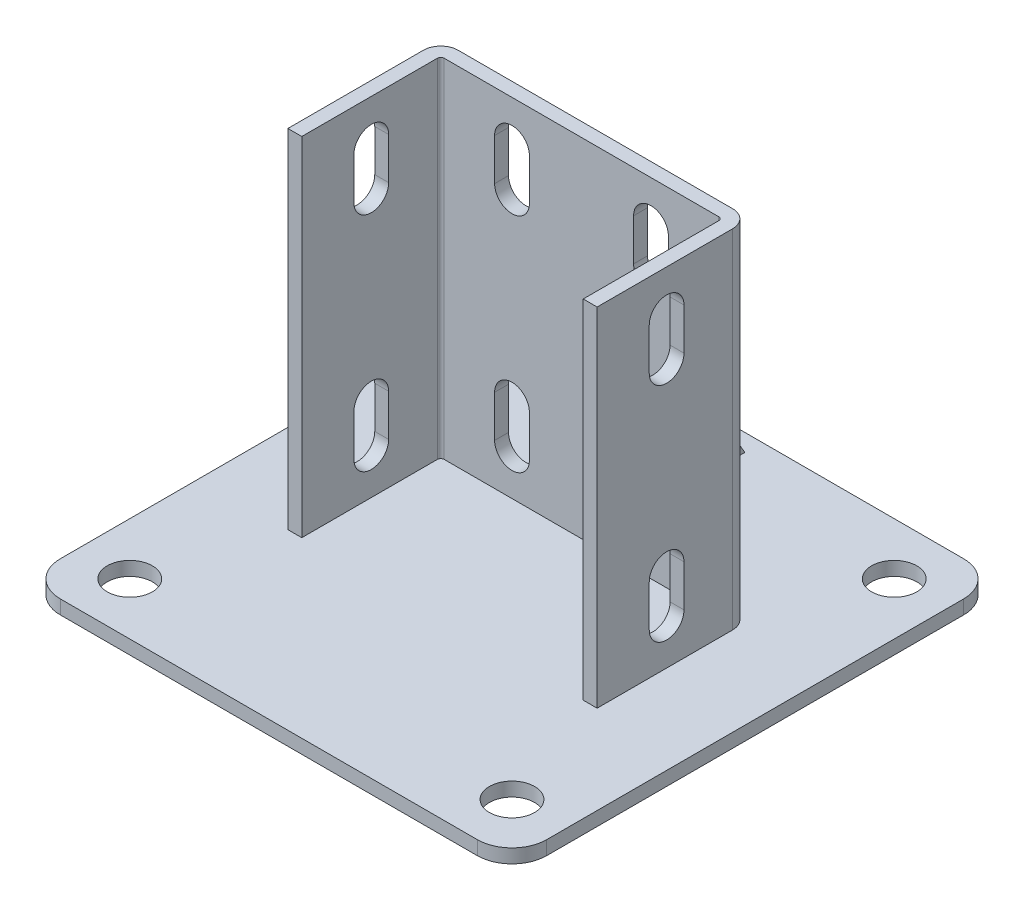
SolidWorks part; units mm, degrees
material "Ст3пс ГОСТ 380-2005"
ref_plane "Спереди" through (0, 0, 0) normal (0, 0, 1) x (1, 0, 0)
ref_plane "Сверху" through (0, 0, 0) normal (0, 1, 0) x (1, 0, 0)
ref_plane "Справа" through (0, 0, 0) normal (1, 0, 0) x (0, 0, -1)
sketch "Эскиз2" plane through (0, 0, 0) normal (0, 1, 0) x (1, 0, 0)
  line L1 (-70, -70) -> (70, -70)
  line L2 (-70, -70) -> (-70, 70)
  line L3 (-70, 70) -> (70, 70)
  line L4 (70, -70) -> (70, 70)
  line L5 (-70, -70) -> (70, 70) construction
  line L6 (-70, 70) -> (70, -70) construction
  point P0 (0, 0)
  dimension "D1" = 140
  dimension "D2" = 140
extrude "Бобышка-Вытянуть1" add sketch "Эскиз2" along normal blind 4
sketch "Эскиз3" plane through (0, 4, 0) normal (0, 1, 0) x (1, 0, 0)
  line L0 (-40.5, -20) -> (-40.5, 20)
  line L1 (-40.5, 20) -> (40.5, 20)
  line L2 (40.5, 20) -> (40.5, -20)
  point P2 (0, 20)
  point P5 (-40.5, 0)
  dimension "D2" = 81
  dimension "D3" = 40
extrude "Вытянуть-Тонкостенный1" add sketch "Эскиз3" along normal offset from surface (100 mm away) 104 thin up to face at (0, 0, 0) thin type one direction reverse wall 4
sketch "Эскиз4" plane through (0, 0, 0) normal (1, 0, 0) x (0, 0, -1)
  line L0 (24, 75.0141) -> (65, 4)
  line L1 (24, 104) -> (24, 4) construction
  line L2 (-70, 4) -> (70, 4) construction
  line L3 (65, 4) -> (24, 4)
  line L4 (24, 4) -> (24, 75.0141)
  line L5 (70, 4) -> (70, 0) construction
  dimension "D1" = 30
  dimension "D2" = 5
extrude "Бобышка-Вытянуть2" add sketch "Эскиз4" along normal mid plane 4
sketch "Эскиз5" plane through (44.5, 0, 0) normal (1, 0, 0) x (0, 0, -1)
  line L0 (0, 92) -> (0, 80) construction
  line L1 (5, 92) -> (5, 80)
  line L2 (-5, 92) -> (-5, 80)
  line L3 (0, 28) -> (0, 16) construction
  line L4 (5, 28) -> (5, 16)
  line L5 (-5, 28) -> (-5, 16)
  line L6 (-20, 104) -> (19, 104) construction
  line L7 (-70, 4) -> (70, 4) construction
  arc A0 (5, 92) -> (-5, 92) centre (0, 92) ccw
  arc A1 (-5, 80) -> (5, 80) centre (0, 80) ccw
  arc A2 (5, 28) -> (-5, 28) centre (0, 28) ccw
  arc A3 (-5, 16) -> (5, 16) centre (0, 16) ccw
  point P3 (0, 86)
  point P8 (0, 22)
  dimension "D2" = 12
  dimension "D4" = 12
  dimension "D1" = 10
  dimension "D3" = 12
extrude "Вырез-Вытянуть1" cut sketch "Эскиз5" against normal through all
sketch "Эскиз6" plane through (0, 4, 0) normal (0, 1, 0) x (1, 0, 0)
  line L0 (-70, 70) -> (-70, -70) construction
  line L1 (55, -55) -> (-55, -55) construction
  line L2 (55, -55) -> (55, 55) construction
  line L3 (55, 55) -> (-55, 55) construction
  line L4 (-55, -55) -> (-55, 55) construction
  line L5 (55, -55) -> (-55, 55) construction
  line L6 (55, 55) -> (-55, -55) construction
  line L7 (70, 70) -> (-70, 70) construction
  circle A0 centre (-55, 55) radius 6.5
  circle A1 centre (-55, -55) radius 6.5
  circle A2 centre (55, 55) radius 6.5
  circle A3 centre (55, -55) radius 6.5
  point P0 (0, 0)
  dimension "D1" = 13
  dimension "D2" = 15
  dimension "D3" = 15
extrude "Вырез-Вытянуть2" cut sketch "Эскиз6" against normal through all
fillet "Скругление1" radius 10 4 edges at (70, 2, 70) (-70, 2, 70) (-70, 2, -70) (70, 2, -70)
sketch "Эскиз8" plane through (0, 0, -24) normal (0, 0, -1) x (-1, 0, 0)
  line L0 (-20, 92) -> (-20, 80) construction
  line L1 (-15, 92) -> (-15, 80)
  line L2 (-25, 92) -> (-25, 80)
  line L3 (-20, 28) -> (-20, 16) construction
  line L4 (-15, 28) -> (-15, 16)
  line L5 (-25, 28) -> (-25, 16)
  line L6 (-39.5, 104) -> (39.5, 104) construction
  line L7 (-60, 4) -> (60, 4) construction
  line L8 (0, 0) -> (0, 104) construction
  line L9 (-60, 0) -> (60, 0) construction
  line L10 (20, 92) -> (20, 80) construction
  line L11 (15, 92) -> (15, 80)
  line L12 (25, 92) -> (25, 80)
  line L13 (20, 28) -> (20, 16) construction
  line L14 (15, 28) -> (15, 16)
  line L15 (25, 28) -> (25, 16)
  arc A0 (-15, 92) -> (-25, 92) centre (-20, 92) ccw
  arc A1 (-25, 80) -> (-15, 80) centre (-20, 80) ccw
  arc A2 (-15, 28) -> (-25, 28) centre (-20, 28) ccw
  arc A3 (-25, 16) -> (-15, 16) centre (-20, 16) ccw
  arc A4 (15, 92) -> (25, 92) centre (20, 92) cw
  arc A5 (25, 80) -> (15, 80) centre (20, 80) cw
  arc A6 (15, 28) -> (25, 28) centre (20, 28) cw
  arc A7 (25, 16) -> (15, 16) centre (20, 16) cw
  point P2 (-20, 86)
  point P7 (-20, 22)
  point P24 (20, 86)
  point P31 (20, 22)
  dimension "D3" = 12
  dimension "D4" = 12
  dimension "D1" = 10
  dimension "D2" = 12
  dimension "D5" = 30
extrude "Вырез-Вытянуть3" cut sketch "Эскиз8" against normal up to next
